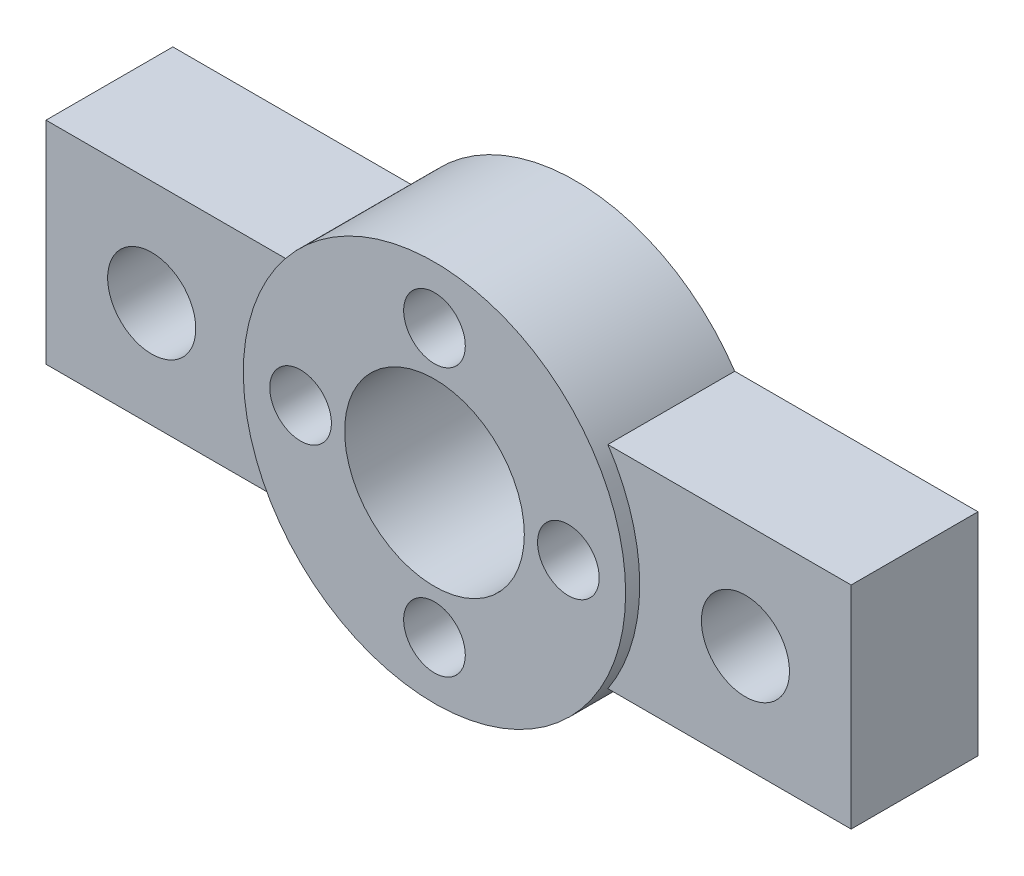
SolidWorks part; units mm, degrees
ref_plane "Front Plane" through (0, 0, 0) normal (0, 0, 1) x (1, 0, 0)
ref_plane "Top Plane" through (0, 0, 0) normal (0, 1, 0) x (1, 0, 0)
ref_plane "Right Plane" through (0, 0, 0) normal (1, 0, 0) x (0, 0, -1)
sketch "Sketch1" plane through (0, 0, 0) normal (0, 0, 1) x (1, 0, 0)
  circle A0 centre (0, 0) radius 5.1
  circle A1 centre (0, 0) radius 10.85
  circle A2 centre (-7.6, 0) radius 1.75
  circle A3 centre (0, 7.6) radius 1.75
  circle A4 centre (7.6, 0) radius 1.75
  circle A5 centre (0, -7.6) radius 1.75
extrude "Boss-Extrude1" add sketch "Sketch1" along normal blind 8
sketch "Sketch2" plane through (0, 0, 0) normal (0, 0, -1) x (-1, 0, 0)
  line L6 (-22.85, -6) -> (-22.85, 6)
  line L7 (22.85, -6) -> (22.85, 6)
  line L8 (-22.85, 6) -> (-9.04, 6)
  line L9 (-22.85, -6) -> (-9.04, -6)
  line L10 (22.85, 6) -> (9.04, 6)
  line L11 (22.85, -6) -> (9.04, -6)
  circle A0 centre (0, 0) radius 10.85 construction
  arc A1 (-9.04, 6) -> (-9.04, -6) centre (0, 0) ccw
  circle A2 centre (16.85, 0) radius 3.55
  circle A3 centre (-16.85, 0) radius 3.55
  arc A4 (9.04, -6) -> (9.04, 6) centre (0, 0) ccw
  point P0 (0, 0)
  point P3 (-10.85, 0)
  point P6 (10.85, 0)
  point P13 (-22.85, 0)
  point P15 (22.85, 0)
  point P23 (20.4, 0)
  point P25 (22.85, 0)
  dimension "D5" = 7.1
  dimension "D3" = 12
  dimension "D4" = 12
extrude "Boss-Extrude3" add sketch "Sketch2" against normal blind 3.2
sketch "Sketch3" plane through (0, 0, 3.2) normal (0, 0, 1) x (1, 0, 0)
  line L0 (-9.04, 6) -> (-22.85, 6)
  line L1 (-22.85, 6) -> (-22.85, -6)
  line L2 (-22.85, -6) -> (-9.04, -6)
  line L3 (9.04, -6) -> (22.85, -6)
  line L4 (22.85, -6) -> (22.85, 6)
  line L5 (22.85, 6) -> (9.04, 6)
  arc A0 (-9.04, 6) -> (-9.04, -6) centre (0, 0) ccw
  arc A1 (9.04, -6) -> (9.04, 6) centre (0, 0) ccw
  circle A2 centre (16.85, 0) radius 2.5
  circle A3 centre (-16.85, 0) radius 2.5
  dimension "D1" = 5
  dimension "D2" = 5
extrude "Boss-Extrude4" add sketch "Sketch3" along normal blind 4
